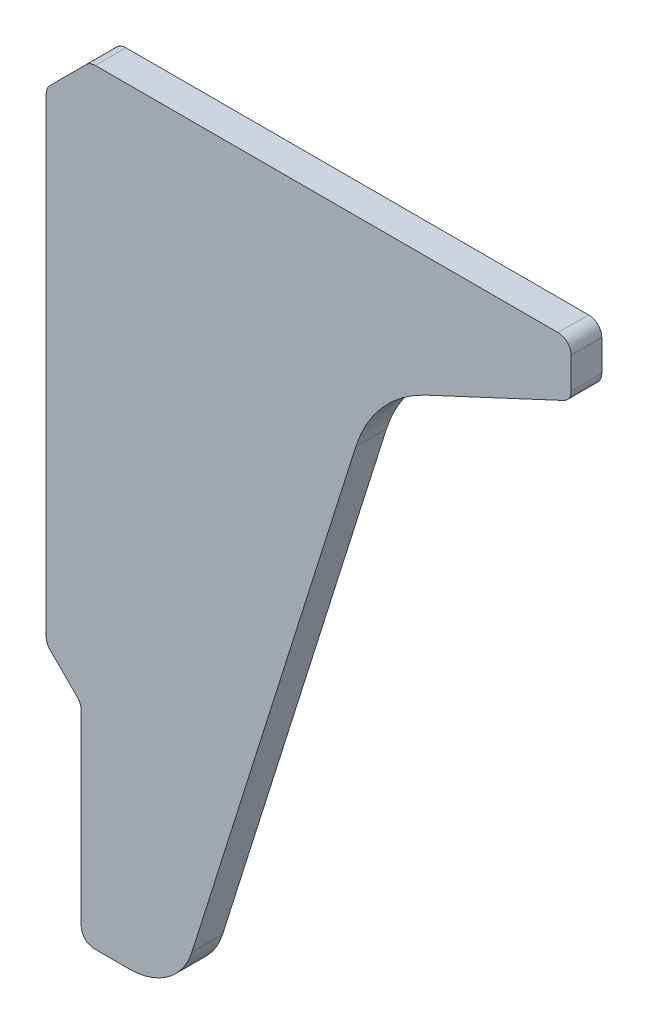
SolidWorks part; units mm, degrees
ref_plane "Front" through (0, 0, 0) normal (0, 0, 1) x (1, 0, 0)
ref_plane "Top" through (0, 0, 0) normal (0, 1, 0) x (1, 0, 0)
ref_plane "Right" through (0, 0, 0) normal (1, 0, 0) x (0, 0, -1)
sketch "Sketch1" plane through (0, 0, 0) normal (0, 0, 1) x (1, 0, 0)
  line L0 (-8, 56.2426) -> (-8, 163.7574)
  line L1 (3.2426, 175) -> (109, 175)
  line L2 (112, 172) -> (112, 164.9112)
  line L3 (110.2679, 162.1923) -> (78.7027, 147.4732)
  line L4 (25.3073, 10.4894) -> (62.7698, 129.3052)
  line L5 (-7.1213, 165.8787) -> (1.1213, 174.1213)
  line L6 (11.0015, 0) -> (3, 0)
  line L7 (0, 3) -> (0, 45.7574)
  line L8 (-7.1213, 54.1213) -> (-0.8787, 47.8787)
  arc A0 (109, 175) -> (112, 172) centre (109, 172) cw
  arc A1 (78.7027, 147.4732) -> (62.7698, 129.3052) centre (91.3813, 120.284) ccw
  arc A2 (11.0015, 0) -> (25.3073, 10.4894) centre (11.0015, 15) ccw
  arc A3 (110.2679, 162.1923) -> (112, 164.9112) centre (109, 164.9112) ccw
  arc A5 (0, 3) -> (3, 0) centre (3, 3) ccw
  arc A6 (-0.8787, 47.8787) -> (0, 45.7574) centre (-3, 45.7574) cw
  arc A7 (-7.1213, 54.1213) -> (-8, 56.2426) centre (-5, 56.2426) cw
  arc A8 (-7.1213, 165.8787) -> (-8, 163.7574) centre (-5, 163.7574) ccw
  arc A9 (1.1213, 174.1213) -> (3.2426, 175) centre (3.2426, 172) cw
  point P1 (2, 175)
  point P5 (22, 0)
  point P7 (112, 175)
  point P18 (112, 163)
  point P26 (0, 47)
  point P29 (-8, 55)
  dimension "D6" = 30
  dimension "D4" = 30
  dimension "D12" = 15
  dimension "D13" = 45
  dimension "D15" = 25
  dimension "D7" = 3
  dimension "D1" = 175
  dimension "D2" = 12
  dimension "D3" = 8
  dimension "D5" = 120
  dimension "D8" = 55
  dimension "D9" = 17.5
  dimension "D10" = 10
  dimension "D11" = 8
extrude "Extrude1" add sketch "Sketch1" along normal blind 7
